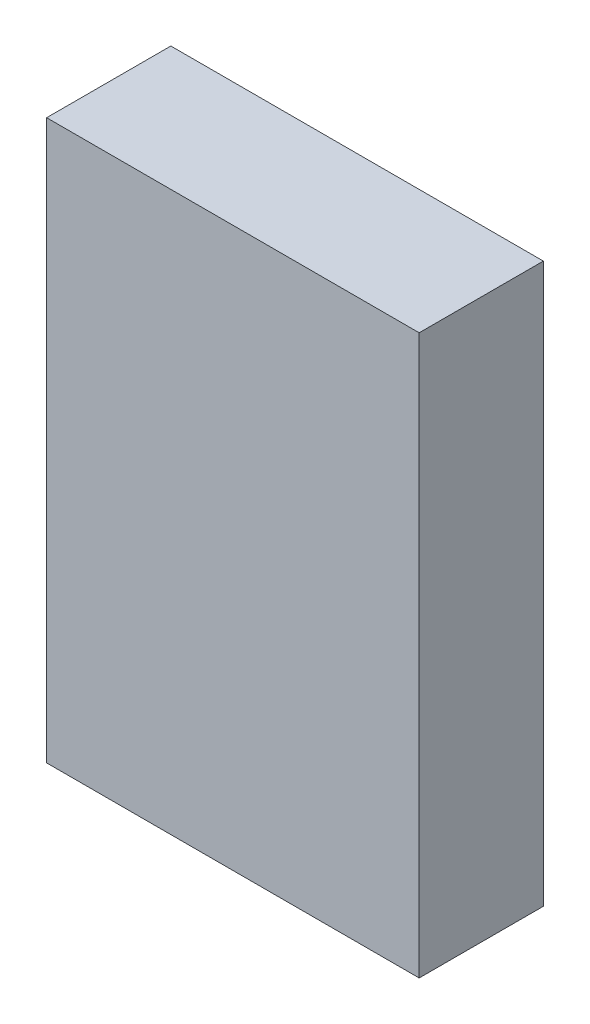
SolidWorks part; units mm, degrees
ref_plane "Plan de face" through (0, 0, 0) normal (0, 0, 1) x (1, 0, 0)
ref_plane "Plan de dessus" through (0, 0, 0) normal (0, 1, 0) x (1, 0, 0)
ref_plane "Plan de droite" through (0, 0, 0) normal (1, 0, 0) x (0, 0, -1)
sketch "Esquisse1" plane through (0, 0, 0) normal (0, 0, 1) x (1, 0, 0)
  line L1 (0, 0) -> (60, 0)
  line L2 (0, 0) -> (0, 90)
  line L3 (0, 90) -> (60, 90)
  line L4 (60, 0) -> (60, 90)
  dimension "D1" = 90
  dimension "D2" = 60
extrude "Boss.-Extru.1" add sketch "Esquisse1" along normal blind 20
